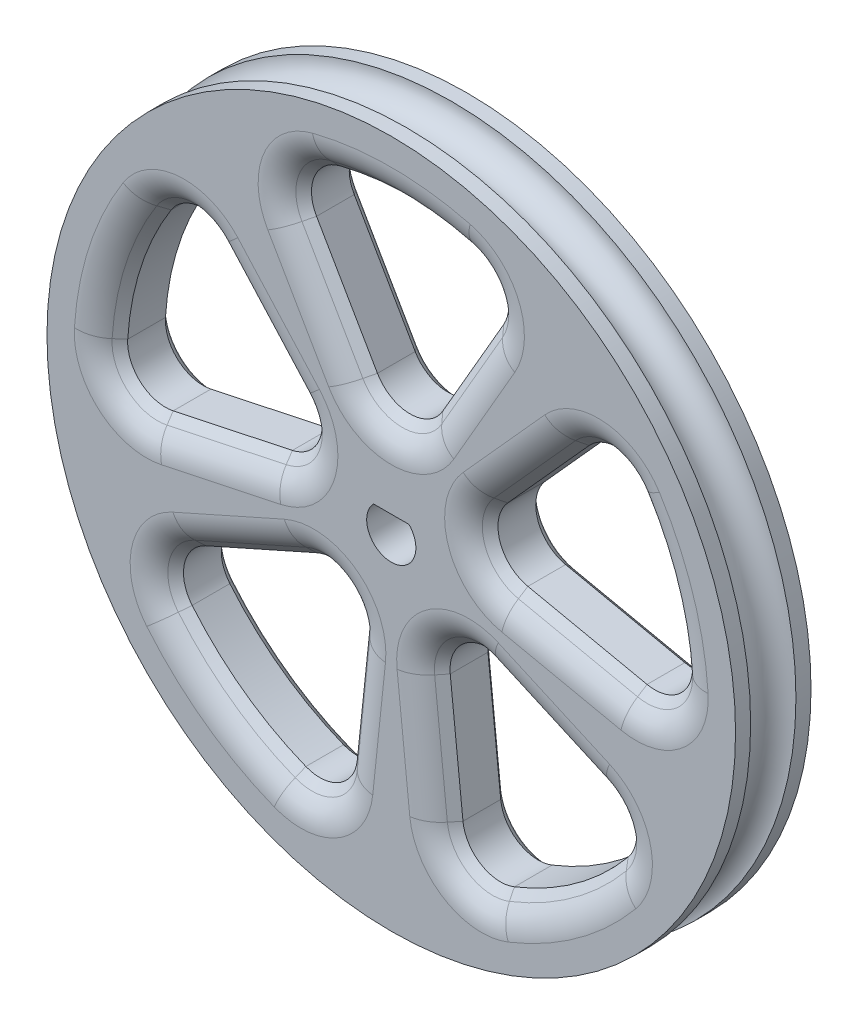
SolidWorks part; units mm, degrees
ref_plane "Front Plane" through (0, 0, 0) normal (0, 0, 1) x (1, 0, 0)
ref_plane "Top Plane" through (0, 0, 0) normal (0, 1, 0) x (1, 0, 0)
ref_plane "Right Plane" through (0, 0, 0) normal (1, 0, 0) x (0, 0, -1)
sketch "Sketch1" plane through (0, 0, 0) normal (0, 0, 1) x (1, 0, 0)
  circle A0 centre (0, 0) radius 23.1775
  dimension "D1" = 46.355
extrude "Boss-Extrude1" add sketch "Sketch1" along normal blind 5.08
sketch "Sketch2" plane through (0, 0, 5.08) normal (0, 0, 1) x (1, 0, 0)
  line L0 (0, 0) -> (0, 19.05) construction
  line L1 (0, 3.81) -> (7.8275, 17.3676)
  line L2 (0, 3.81) -> (-7.8275, 17.3676)
  circle A0 centre (0, 0) radius 19.05 construction
  arc A1 (7.8275, 17.3676) -> (-7.8275, 17.3676) centre (0, 0) ccw
  dimension "D1" = 38.1
  dimension "D2" = 30
  dimension "D3" = 3.81
extrude "Cut-Extrude3" cut sketch "Sketch2" against normal up to surface (5.08 mm away) contours L1 A1 L2 up to face at (23.1775, 0, 0)
sketch3d "3DSketch1"
  line L0 (0, 0, 0) -> (0, 0, -15.5366) construction
fillet "Fillet3" radius 2.54 3 edges at (0, 3.81, 2.54) (-7.8275, 17.3676, 2.54) (7.8275, 17.3676, 2.54)
chamfer "Chamfer2" distance 1.27 angle 45 12 edges at (6.4421, 16.9773, 5.08) (4.2501, 11.1713, 5.08) (0, 6.35, 5.08) (-4.2501, 11.1713, 5.08) (0, 19.05, 5.08) (-6.4421, 16.9773, 5.08) (6.4421, 16.9773, 0) (4.2501, 11.1713, 0) (0, 6.35, 0) (-4.2501, 11.1713, 0) (-6.4421, 16.9773, 0) (0, 19.05, 0)
pattern_circular "CirPattern3" count 5 every 72 about axis through (0, 0, 0) along (0, 0, 1) of "Chamfer2", "Cut-Extrude3", "Fillet3"
sketch "Sketch5" plane through (0, 0, 5.08) normal (0, 0, 1) x (1, 0, 0)
  line L0 (-1.1979, 1.1437) -> (1.1979, 1.1437)
  circle A0 centre (0, 0) radius 1.6563 construction
  arc A1 (1.1979, 1.1437) -> (-1.1979, 1.1437) centre (0, 0) cw
  point P5 (0, -1.6563)
  dimension "D1" = 1.6563
  dimension "D2" = 2.8
extrude "Cut-Extrude4" cut sketch "Sketch5" against normal up to surface (5.08 mm away) contours A1 L0 up to face at (12.9046, 4.1929, 0)
fillet "Fillet4" radius 2.54 60 edges at (-7.6128, 17.4696, 5.08) (-5.3499, 10.5363, 5.08) (0, 5.08, 5.08) (5.3499, 10.5363, 5.08) (7.6128, 17.4696, 5.08) (0, 20.32, 5.08) (-1.8649, -11.6687, 5.08) (-2.9859, -4.1098, 5.08) (-10.5213, -5.3795, 5.08) (-16.4273, -9.6586, 5.08) (-11.9438, -16.4392, 5.08) (-14.2621, 12.6386, 5.08) (-19.3255, 6.2792, 5.08) (-18.9671, -1.8418, 5.08) (-11.6738, -1.8322, 5.08) (-4.8314, 1.5698, 5.08) (-2.9859, -4.1098, 0) (-1.8649, -11.6687, 0) (-4.1095, -18.6079, 0) (-11.9438, -16.4392, 0) (-16.4273, -9.6586, 0) (-8.3674, 8.344, 0) (-4.8314, 1.5698, 0) (-11.6738, -1.8322, 0) (-18.9671, -1.8418, 0) (-19.3255, 6.2792, 0) (0, 20.32, 0) (7.6128, 17.4696, 0) (5.3499, 10.5363, 0) (0, 5.08, 0) (-5.3499, 10.5363, 0) (-4.1095, -18.6079, 5.08) (-8.3674, 8.344, 5.08) (-10.5213, -5.3795, 0) (-14.2621, 12.6386, 0) (-7.6128, 17.4696, 0) (16.4273, -9.6586, 0) (11.9438, -16.4392, 0) (4.1095, -18.6079, 0) (1.8649, -11.6687, 0) (2.9859, -4.1098, 0) (8.3674, 8.344, 0) (14.2621, 12.6386, 0) (19.3255, 6.2792, 0) (18.9671, -1.8418, 0) (11.6738, -1.8322, 0) (1.8649, -11.6687, 5.08) (4.1095, -18.6079, 5.08) (11.9438, -16.4392, 5.08) (16.4273, -9.6586, 5.08) (10.5213, -5.3795, 5.08) (4.8314, 1.5698, 5.08) (11.6738, -1.8322, 5.08) (18.9671, -1.8418, 5.08) (19.3255, 6.2792, 5.08) (14.2621, 12.6386, 5.08) (10.5213, -5.3795, 0) (4.8314, 1.5698, 0) (2.9859, -4.1098, 5.08) (8.3674, 8.344, 5.08)
sketch "Sketch7" plane through (0, 0, 0) normal (0, 1, 0) x (1, 0, 0)
  line L0 (-23.1775, 0) -> (-23.1775, -5.08) construction
  line L1 (-23.1775, -4.064) -> (-23.1775, -1.016)
  circle A0 centre (-23.1775, -2.54) radius 1.524 construction
  arc A1 (-23.1775, -1.016) -> (-23.1775, -4.064) centre (-23.1775, -2.54) cw
  dimension "D1" = 3.048
revolve "Cut-Revolve1" cut sketch "Sketch7" angle 360 about L0
equation "\"D1@Sketch5\"=(3.25mm + .0625mm)/2"
